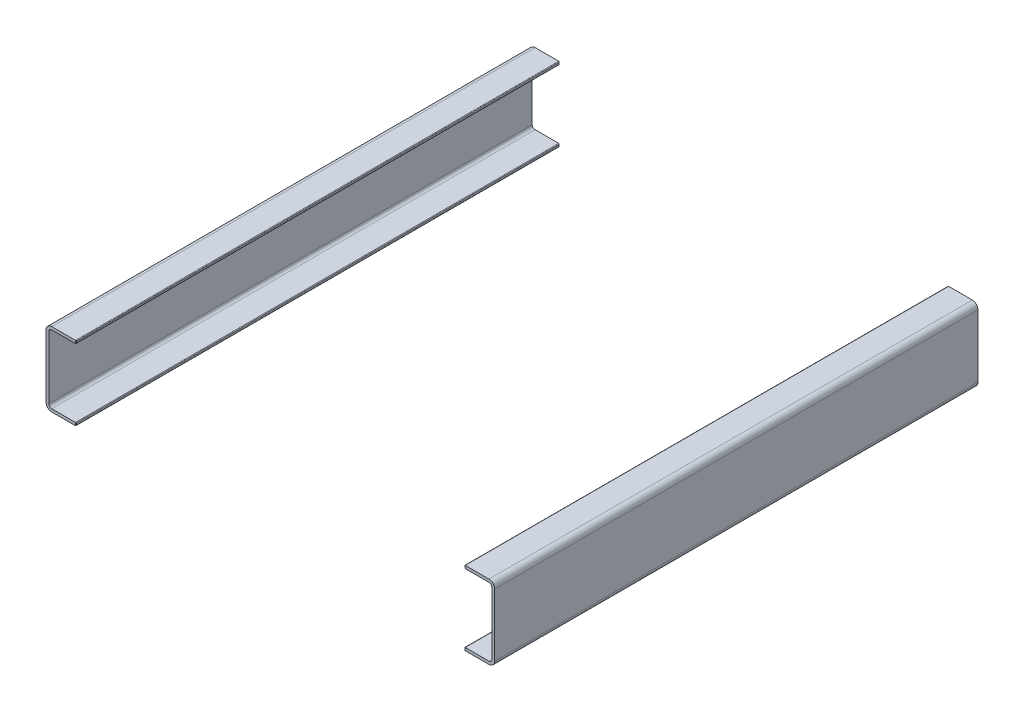
SolidWorks part; units mm, degrees
ref_plane "Front Plane" through (0, 0, 0) normal (0, 0, 1) x (1, 0, 0)
ref_plane "Top Plane" through (0, 0, 0) normal (0, 1, 0) x (1, 0, 0)
ref_plane "Right Plane" through (0, 0, 0) normal (1, 0, 0) x (0, 0, -1)
ref_plane "Plane2" through (123, 0, 0) normal (-1, 0, 0) x (0, 0, 1)
sketch "Sketch6" plane through (123, 0, 0) normal (-1, 0, 0) x (0, 0, 1)
  line L0 (153, 23.4) -> (-153, 23.4)
  line L1 (-153, 23.4) -> (-153, -23.4)
  line L2 (-153, -23.4) -> (153, -23.4)
  line L3 (153, -23.4) -> (153, 23.4)
  line L4 (0, -23.4) -> (0, 0) construction
  line L5 (-153, 0) -> (0, 0) construction
  line L6 (0, 0) -> (153, 0) construction
  line L7 (0, 0) -> (0, 23.4) construction
  dimension "D1" = 306
  dimension "D2" = 46.8
extrude "Boss-Extrude2" add sketch "Sketch6" against normal blind 19 separate body
sketch "Sketch7" plane through (0, 0, 153) normal (0, 0, 1) x (1, 0, 0)
  line L0 (123, -21.6) -> (140.2, -21.6)
  line L1 (140.2, -21.6) -> (140.2, 21.6)
  line L2 (140.2, 21.6) -> (123, 21.6)
  line L3 (123, 21.6) -> (123, -21.6)
extrude "Cut-Extrude2" cut sketch "Sketch7" against normal through all
fillet "Fillet4" radius 0.4 8 edges at (123, -22.5, -153) (123, -21.6, 0) (123, -23.4, 0) (123, -22.5, 153) (123, 21.6, 0) (123, 22.5, 153) (123, 22.5, -153) (123, 23.4, 0)
fillet "Fillet5" radius 1.8 2 edges at (140.2, 21.6, 0) (140.2, -21.6, 0)
fillet "Fillet6" radius 3.6 2 edges at (142, -23.4, 0) (142, 23.4, 0)
ref_plane "Plane3" through (-123, 0, 0) normal (1, 0, 0) x (0, 0, -1)
sketch "Sketch12" plane through (-123, 0, 0) normal (1, 0, 0) x (0, 0, -1)
  line L0 (-153, 23.4) -> (-153, -23.4)
  line L1 (-153, -23.4) -> (153, -23.4)
  line L2 (153, -23.4) -> (153, 23.4)
  line L3 (153, 23.4) -> (-153, 23.4)
  line L4 (-153, -23.4) -> (-153, 23.4) construction
  line L5 (153, 23.4) -> (153, -23.4) construction
  line L6 (153, -23.4) -> (-153, -23.4) construction
  line L7 (-153, 23.4) -> (153, 23.4) construction
extrude "Boss-Extrude3" add sketch "Sketch12" against normal blind 19 separate body
sketch "Sketch13" plane through (0, 0, 153) normal (0, 0, 1) x (1, 0, 0)
  line L0 (-123, -21.6) -> (-123, 21.6)
  line L1 (-123, 21.6) -> (-140.2, 21.6)
  line L2 (-140.2, 21.6) -> (-140.2, -21.6)
  line L3 (-140.2, -21.6) -> (-123, -21.6)
extrude "Cut-Extrude3" cut sketch "Sketch13" against normal through all
fillet "Fillet7" radius 0.4 8 edges at (-123, 23.4, 0) (-123, 22.5, 153) (-123, 22.5, -153) (-123, 21.6, 0) (-123, -22.5, -153) (-123, -23.4, 0) (-123, -22.5, 153) (-123, -21.6, 0)
fillet "Fillet8" radius 1.8 2 edges at (-140.2, 21.6, 0) (-140.2, -21.6, 0)
fillet "Fillet9" radius 3.6 2 edges at (-142, -23.4, 0) (-142, 23.4, 0)
